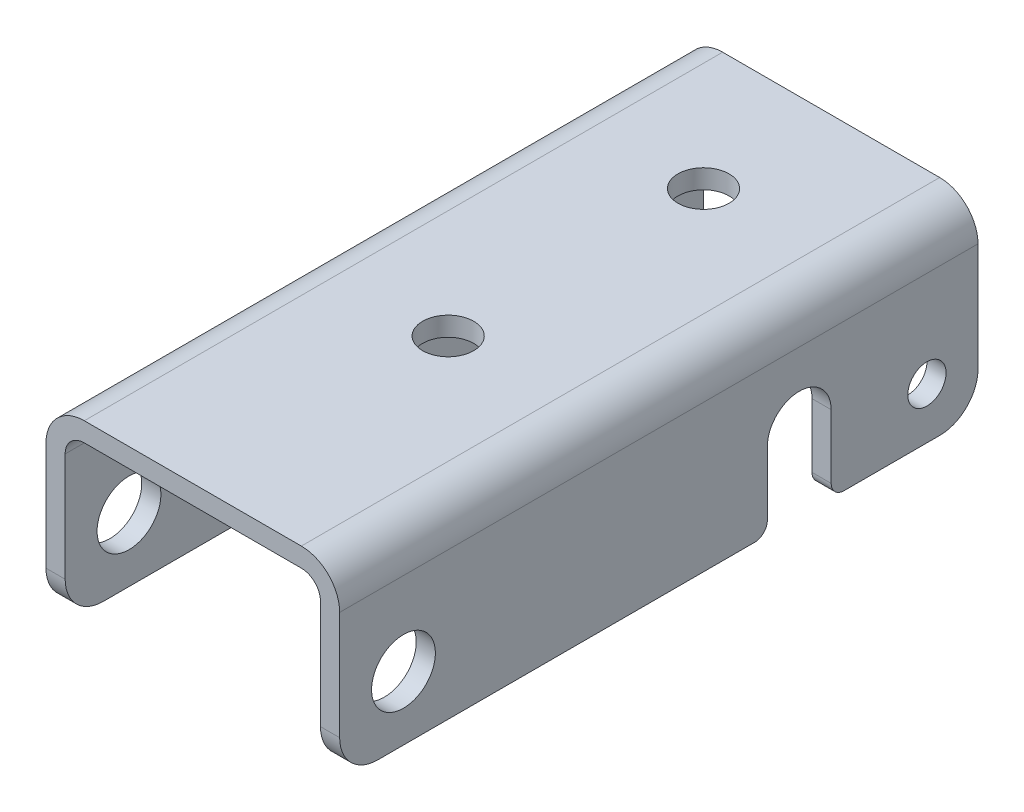
SolidWorks part; units mm, degrees
material "AISI 304"
ref_plane "Front" through (0, 0, 0) normal (0, 0, 1) x (1, 0, 0)
ref_plane "Top" through (0, 0, 0) normal (0, 1, 0) x (1, 0, 0)
ref_plane "Right" through (0, 0, 0) normal (1, 0, 0) x (0, 0, -1)
sketch "Sketch1" plane through (0, 0, 0) normal (0, 0, 1) x (1, 0, 0)
  line L0 (0, 0) -> (0, 52.1017) construction
  line L1 (11.5, 0) -> (11.5, 11.5)
  line L2 (-11.5, 0) -> (-11.5, 11.5)
  line L3 (-11.5, 0) -> (-10, 0)
  line L4 (-11.5, 0) -> (-11.5, 52.1017) construction
  line L5 (-8.5, 14.5) -> (8.5, 14.5)
  line L6 (11.5, 0) -> (11.5, 52.1017) construction
  line L7 (-11.5, 14.5) -> (11.5, 14.5) construction
  line L8 (-10, 0) -> (-10, 11.5)
  line L9 (-8.5, 13) -> (8.5, 13)
  line L10 (10, 0) -> (10, 11.5)
  line L11 (10, 0) -> (11.5, 0)
  line L13 (-11.5, 0) -> (11.5, 0) construction
  arc A0 (11.5, 11.5) -> (8.5, 14.5) centre (8.5, 11.5) ccw
  arc A1 (-11.5, 11.5) -> (-8.5, 14.5) centre (-8.5, 11.5) cw
  arc A2 (-10, 11.5) -> (-8.5, 13) centre (-8.5, 11.5) cw
  arc A3 (10, 11.5) -> (8.5, 13) centre (8.5, 11.5) ccw
  dimension "D3" = 3
  dimension "D1" = 11.5
  dimension "D2" = 11.5
  dimension "D4" = 14.5
  dimension "D5" = 1.5
extrude "Boss-Extrude1" add sketch "Sketch1" along normal mid plane 50
fillet "Fillet1" radius 3 4 edges at (10.75, 0, 25) (-10.75, 0, 25) (-10.75, 0, -25) (10.75, 0, -25)
sketch "Sketch2" plane through (11.5, 0, 0) normal (1, 0, 0) x (0, 0, -1)
  line L1 (8.5, 0) -> (8.5, 6)
  line L2 (13.5, 3) -> (13.5, 11.5)
  line L3 (13.5, 0) -> (13.5, 6)
  line L6 (-22, 0) -> (22, 0) construction
  line L7 (-25, 8.5) -> (25, 8.5)
  line L8 (8.5, 8.5) -> (13.5, 8.5) construction
  line L9 (8.5, 0) -> (13.5, 0)
  line L10 (8.5, 3) -> (8.5, 11.5) construction
  line L11 (13.5, 3) -> (13.5, 11.5) construction
  arc A1 (13.5, 6) -> (8.5, 6) centre (11, 6) ccw
  dimension "D1" = 11.5
  dimension "D2" = 5
  dimension "D3" = 6
extrude "Cut-Extrude1" cut sketch "Sketch2" against normal through all
fillet "Fillet2" radius 1 4 edges at (-10.75, 0, -13.5) (-10.75, 0, -8.5) (10.75, 0, -13.5) (10.75, 0, -8.5)
sketch "Sketch3" plane through (11.5, 0, 0) normal (1, 0, 0) x (0, 0, -1)
  line L2 (-22, 5) -> (7.5, 5)
  line L3 (-20, 5) -> (7.5, 5) construction
  line L5 (-20, 3) -> (-20, 11.5)
  line L6 (-20, 5) -> (-20, 11.5) construction
  circle A0 centre (-20, 5) radius 2.5
  dimension "D3" = 5
  dimension "D1" = 5
  dimension "D2" = 5
extrude "Cut-Extrude2" cut sketch "Sketch3" against normal through all
sketch "Sketch4" plane through (11.5, 0, 0) normal (1, 0, 0) x (0, 0, -1)
  line L2 (14.5, 4) -> (22, 4)
  line L3 (14.5, 4) -> (21, 4) construction
  line L5 (21, 3) -> (21, 11.5)
  line L6 (21, 4) -> (21, 11.5) construction
  circle A0 centre (21, 4) radius 1.5
  dimension "D3" = 3
  dimension "D1" = 4
  dimension "D2" = 4
extrude "Cut-Extrude3" cut sketch "Sketch4" against normal through all
sketch "Sketch5" plane through (0, 14.5, 0) normal (0, 1, 0) x (1, 0, 0)
  line L1 (8.5, -5) -> (-8.5, -5) construction
  line L2 (8.5, 15) -> (-8.5, 15)
  line L3 (8.5, 15) -> (-8.5, 15) construction
  circle A0 centre (0, 15) radius 2
  circle A1 centre (0, -5) radius 2
  dimension "D3" = 4
  dimension "D4" = 4
  dimension "D1" = 10
  dimension "D2" = 20
extrude "Cut-Extrude4" cut sketch "Sketch5" against normal blind 50
